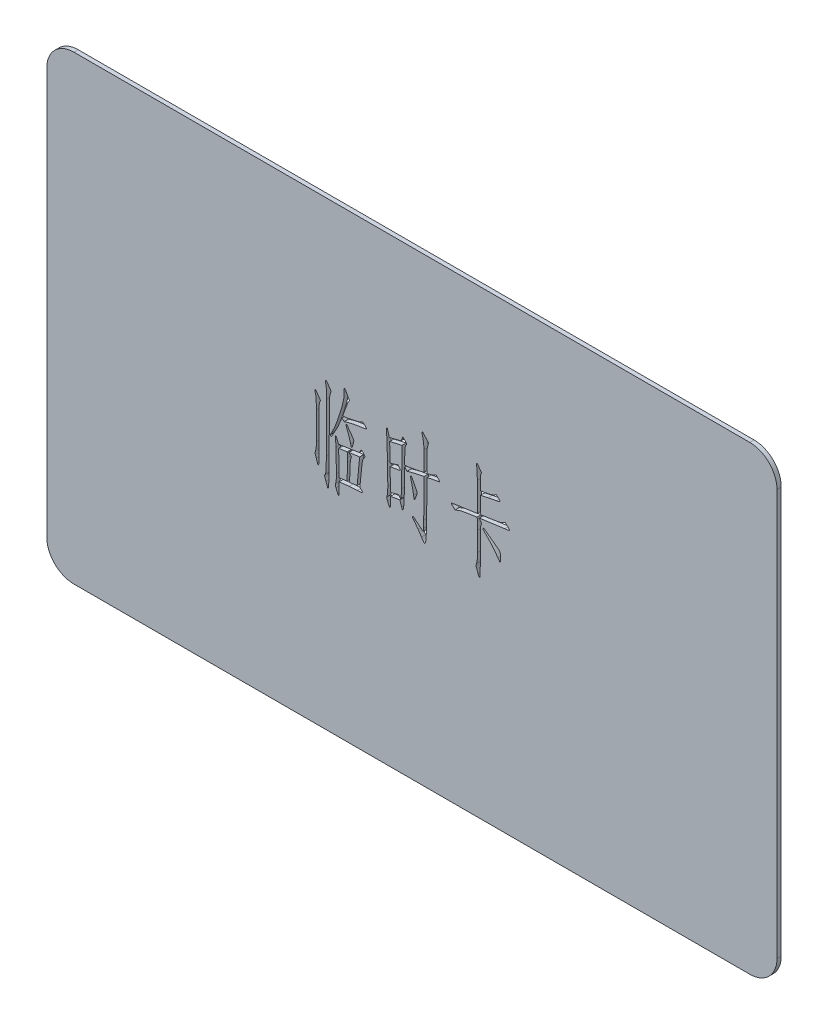
SolidWorks part; units mm, degrees
ref_plane "前视基准面" through (0, 0, 0) normal (0, 0, 1) x (1, 0, 0)
ref_plane "上视基准面" through (0, 0, 0) normal (0, 1, 0) x (1, 0, 0)
ref_plane "右视基准面" through (0, 0, 0) normal (1, 0, 0) x (0, 0, -1)
sketch "草图1" plane through (0, 0, 0) normal (0, 0, 1) x (1, 0, 0)
  line L1 (0, 0) -> (85.6, 0)
  line L2 (0, 0) -> (0, 54)
  line L3 (0, 54) -> (85.6, 54)
  line L4 (85.6, 0) -> (85.6, 54)
  dimension "D1" = 85.6
  dimension "D2" = 54
extrude "凸台-拉伸1" add sketch "草图1" along normal blind 0.5
sketch "草图2" plane through (0, 0, 0.5) normal (0, 0, 1) x (1, 0, 0)
  text T0 "临时卡" font "汉仪长仿宋体" height 8
extrude "切除-拉伸1" cut sketch "草图2" against normal blind 0.5
fillet "圆角1" radius 3.18 1 edges at (0, 54, 0.25)
fillet "圆角2" radius 3.18 3 edges at (85.6, 54, 0.25) (85.6, 0, 0.25) (0, 0, 0.25)
